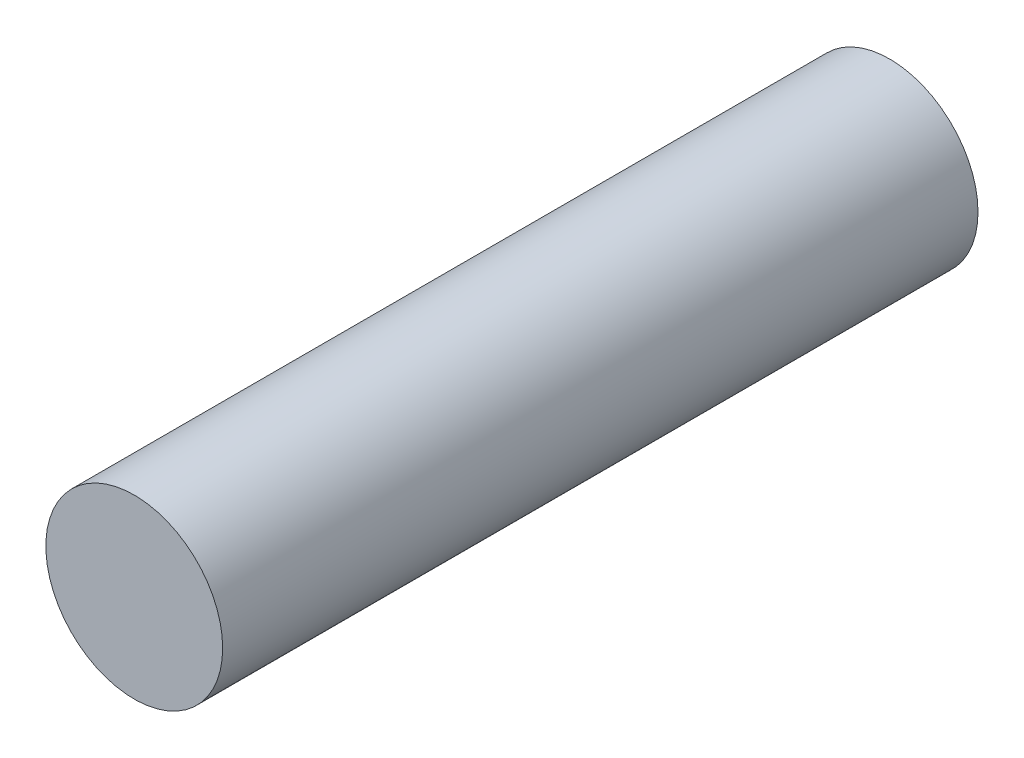
SolidWorks part; units mm, degrees
ref_plane "Front Plane" through (0, 0, 0) normal (0, 0, 1) x (1, 0, 0)
ref_plane "Top Plane" through (0, 0, 0) normal (0, 1, 0) x (1, 0, 0)
ref_plane "Right Plane" through (0, 0, 0) normal (1, 0, 0) x (0, 0, -1)
sketch "Sketch1" plane through (0, 0, 0) normal (0, 0, 1) x (1, 0, 0)
  circle A0 centre (0, 0) radius 5.15
  dimension "D1" = 10.3
extrude "Extrude1" add sketch "Sketch1" along normal blind 44
